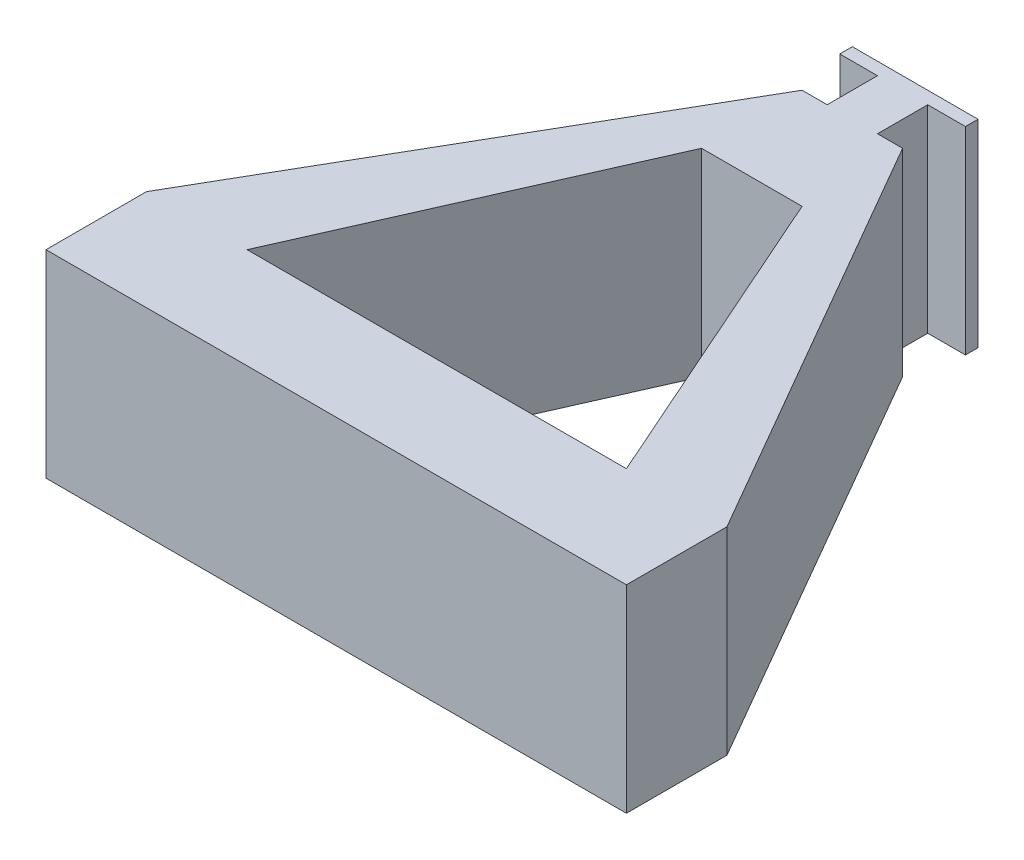
SolidWorks part; units mm, degrees
ref_plane "Płaszczyzna przednia" through (0, 0, 0) normal (0, 0, 1) x (1, 0, 0)
ref_plane "Płaszczyzna górna" through (0, 0, 0) normal (0, 1, 0) x (1, 0, 0)
ref_plane "Płaszczyzna prawa" through (0, 0, 0) normal (1, 0, 0) x (0, 0, -1)
sketch "Sketch1" plane through (0, 0, 0) normal (0, 1, 0) x (1, 0, 0)
  line L0 (-25.4, 165.4) -> (-146.6436, -44.6)
  line L4 (0, 140) -> (-121.2436, -70) construction
  line L5 (-121.2436, -70) -> (121.2436, -70) construction
  line L6 (121.2436, -70) -> (0, 140) construction
  line L7 (-25.4, 165.4) -> (25.4, 165.4)
  line L8 (-25.4, 165.4) -> (-25.4, 114.6)
  line L9 (-25.4, 114.6) -> (25.4, 114.6)
  line L10 (25.4, 165.4) -> (25.4, 114.6)
  line L11 (-25.4, 165.4) -> (25.4, 114.6) construction
  line L12 (-25.4, 114.6) -> (25.4, 165.4) construction
  line L13 (95.8436, -95.4) -> (146.6436, -95.4)
  line L14 (95.8436, -95.4) -> (95.8436, -44.6)
  line L15 (95.8436, -44.6) -> (146.6436, -44.6)
  line L16 (146.6436, -95.4) -> (146.6436, -44.6)
  line L17 (95.8436, -95.4) -> (146.6436, -44.6) construction
  line L18 (95.8436, -44.6) -> (146.6436, -95.4) construction
  line L19 (-146.6436, -44.6) -> (-95.8436, -44.6)
  line L20 (-146.6436, -44.6) -> (-146.6436, -95.4)
  line L21 (-146.6436, -95.4) -> (-95.8436, -95.4)
  line L22 (-95.8436, -44.6) -> (-95.8436, -95.4)
  line L23 (-146.6436, -44.6) -> (-95.8436, -95.4) construction
  line L24 (-146.6436, -95.4) -> (-95.8436, -44.6) construction
  line L29 (25.4, 165.4) -> (146.6436, -44.6)
  line L30 (95.8436, -95.4) -> (-95.8436, -95.4)
  line L31 (-95.8436, -44.6) -> (95.8436, -44.6)
  line L36 (-25.4, 114.6) -> (-95.8436, -44.6)
  line L37 (25.4, 114.6) -> (95.8436, -44.6)
  line L42 (0, 190.8) -> (31.75, 190.8) construction
  line L43 (0, 165.4) -> (0, 190.8) construction
  line L44 (0, 190.8) -> (-31.75, 190.8) construction
  line L46 (31.75, 190.8) -> (-31.75, 190.8)
  line L47 (31.75, 190.8) -> (31.75, 197.15)
  line L48 (31.75, 197.15) -> (-31.75, 197.15)
  line L49 (-31.75, 190.8) -> (-31.75, 197.15)
  line L50 (-12.7, 190.8) -> (12.7, 190.8)
  line L51 (-12.7, 190.8) -> (-12.7, 165.4)
  line L52 (-12.7, 165.4) -> (12.7, 165.4)
  line L53 (12.7, 190.8) -> (12.7, 165.4)
  line L54 (-12.7, 190.8) -> (12.7, 165.4) construction
  line L55 (-12.7, 165.4) -> (12.7, 190.8) construction
  circle A0 centre (0, 0) radius 70 construction
  point P24 (0, 178.1)
  dimension "D2" = 50.8
  dimension "D1" = 50.8
  dimension "D3" = 50.8
  dimension "D4" = 50.8
  dimension "D5" = 50.8
  dimension "D6" = 50.8
  dimension "D7" = 25.4
  dimension "D8" = 31.75
  dimension "D9" = 31.75
  dimension "D10" = 63.5
  dimension "D11" = 6.35
  dimension "D12" = 25.4
extrude "Boss-Extrude1" add sketch "Sketch1" along normal blind 100
